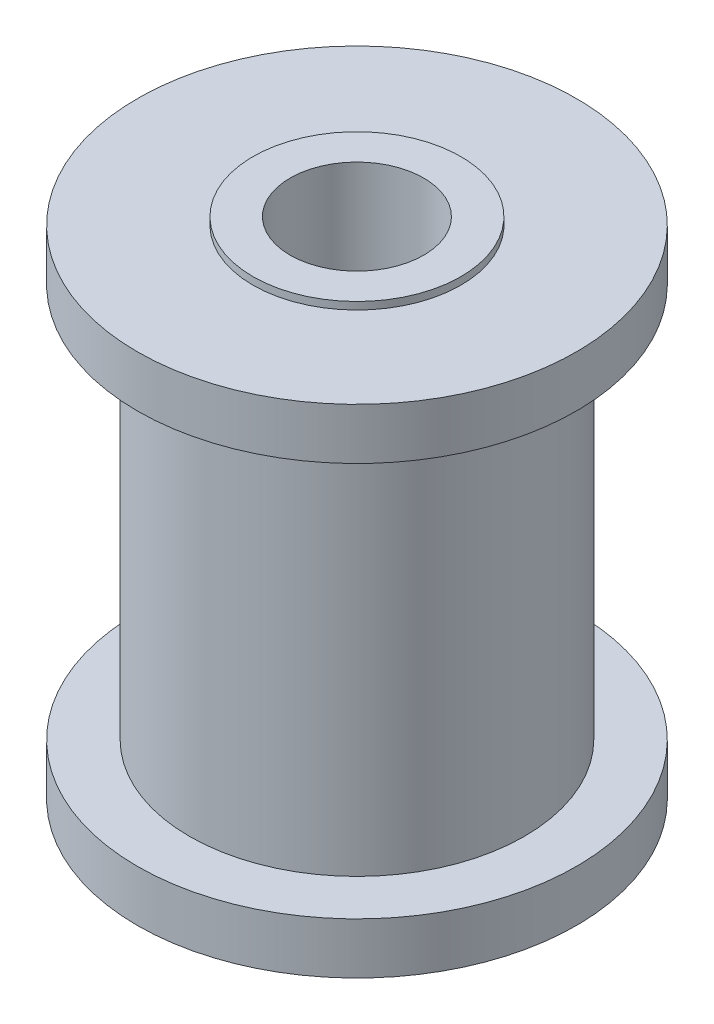
SolidWorks part; units mm, degrees
ref_plane "Front Plane" through (0, 0, 0) normal (0, 0, 1) x (1, 0, 0)
ref_plane "Top Plane" through (0, 0, 0) normal (0, 1, 0) x (1, 0, 0)
ref_plane "Right Plane" through (0, 0, 0) normal (1, 0, 0) x (0, 0, -1)
ref_axis "Axis1" through (0, 55, 0) along (0, -1, 0)
sketch "Sketch2" plane through (0, 0, 0) normal (1, 0, 0) x (0, 0, -1)
  line L0 (2.286, 0.9906) -> (3.556, 0.9906)
  line L1 (3.556, 0.9906) -> (3.556, 0.7366)
  line L2 (3.556, 0.7366) -> (7.5057, 0.7366)
  line L3 (7.5057, 0.7366) -> (7.5057, -1.016)
  line L5 (5.7277, -1.016) -> (5.7277, -14.5034)
  line L7 (7.5057, -14.5034) -> (7.5057, -16.256)
  line L8 (7.5057, -16.256) -> (3.556, -16.256)
  line L9 (3.556, -16.256) -> (3.556, -16.51)
  line L10 (3.556, -16.51) -> (2.286, -16.51)
  line L11 (5.7277, -1.016) -> (7.5057, -1.016)
  line L13 (2.286, -16.51) -> (2.286, 0.9906)
  line L14 (0, 55) -> (0, -55) construction
  line L17 (5.7277, -14.5034) -> (7.5057, -14.5034)
  dimension "D1" = 17.5006
  dimension "D2" = 2.286
  dimension "D3" = 7.5057
  dimension "D4" = 1.27
  dimension "D5" = 0.254
  dimension "D6" = 13.4874
  dimension "D7" = 5.7277
revolve "Revolve1" add sketch "Sketch2" angle 360 about axis through (0, 55, 0) along (0, -1, 0)
